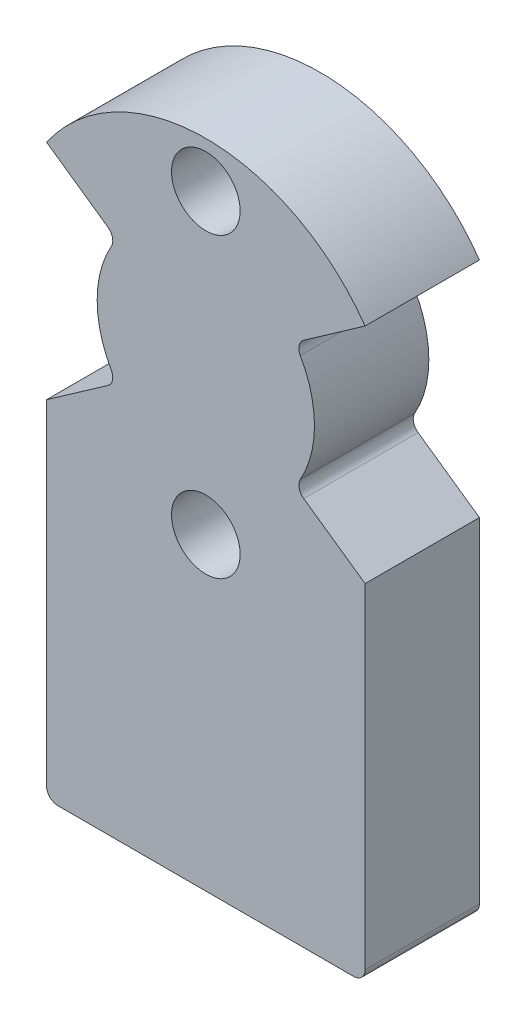
SolidWorks part; units mm, degrees
material "Thornel Mat VMA"
ref_plane "前视基准面" through (0, 0, 0) normal (0, 0, 1) x (1, 0, 0)
ref_plane "上视基准面" through (0, 0, 0) normal (0, 1, 0) x (1, 0, 0)
ref_plane "右视基准面" through (0, 0, 0) normal (1, 0, 0) x (0, 0, -1)
sketch "草图1" plane through (0, 0, 0) normal (0, 0, 1) x (1, 0, 0)
  circle A0 centre (0, 0) radius 8.5
  dimension "D1" = 17
extrude "凸台-拉伸1" add sketch "草图1" along normal blind 5
sketch "草图2" plane through (0, 0, 5) normal (0, 0, 1) x (1, 0, 0)
  circle A0 centre (0, 0) radius 6.5 construction
  circle A1 centre (0, 6.5) radius 1.5
  circle A2 centre (0, -6.5) radius 1.5
  dimension "D1" = 13
  dimension "D2" = 3
extrude "切除-拉伸1" cut sketch "草图2" against normal blind 5
sketch "草图3" plane through (0, 0, 0) normal (0, 0, -1) x (-1, 0, 0)
  line L0 (0, 0) -> (11.6987, 0) construction
  line L1 (0, 0) -> (6.9628, 4.8754)
  line L2 (0, 0) -> (6.9628, -4.8754)
  circle A0 centre (0, 0) radius 4.75
  circle A1 centre (0, 0) radius 8.5
  circle M17 centre (0, 0) radius 8.5
  dimension "D1" = 9.5
  dimension "D2" = 17
  dimension "D3" = 35
  dimension "D4" = 35
extrude "切除-拉伸2" cut sketch "草图3" against normal through all contours A0 L0 A1 L1 | L0 A0 L2 M17
mirror "镜向1" about plane through (0, 0, 0) normal (1, 0, 0) of "切除-拉伸2"
sketch "草图4" plane through (0, 0, 0) normal (0, 0, -1) x (-1, 0, 0)
  line L2 (-6.9628, 4.8754) -> (-6.9628, -20)
  line L3 (-6.9628, -20) -> (6.9628, -20)
  line L4 (6.9628, 4.8754) -> (6.9628, -20)
  line L5 (-2.7947, 8.0274) -> (6.9628, -20) construction
  line L6 (-6.9628, -20) -> (2.7947, 8.0274) construction
  circle A0 centre (0, 0) radius 8.5
  arc M9 (-6.9628, -4.8754) -> (6.9628, -4.8754) centre (0, 0) ccw
  dimension "D1" = 17
  dimension "D2" = 13.9256
  dimension "D3" = 20
extrude "凸台-拉伸2" add sketch "草图4" against normal blind 5 separate body contours L4 L2 L3 M9 | A0
combine bodies "组合1" operation type add bodies to combine 109 110 110
fillet "圆角1" radius 0.5 4 edges at (-3.891, -2.7245, 2.5) (-3.891, 2.7245, 2.5) (3.891, 2.7245, 2.5) (3.891, -2.7245, 2.5)
fillet "圆角2" radius 0.5 2 edges at (6.9628, -20, 2.5) (-6.9628, -20, 2.5)
